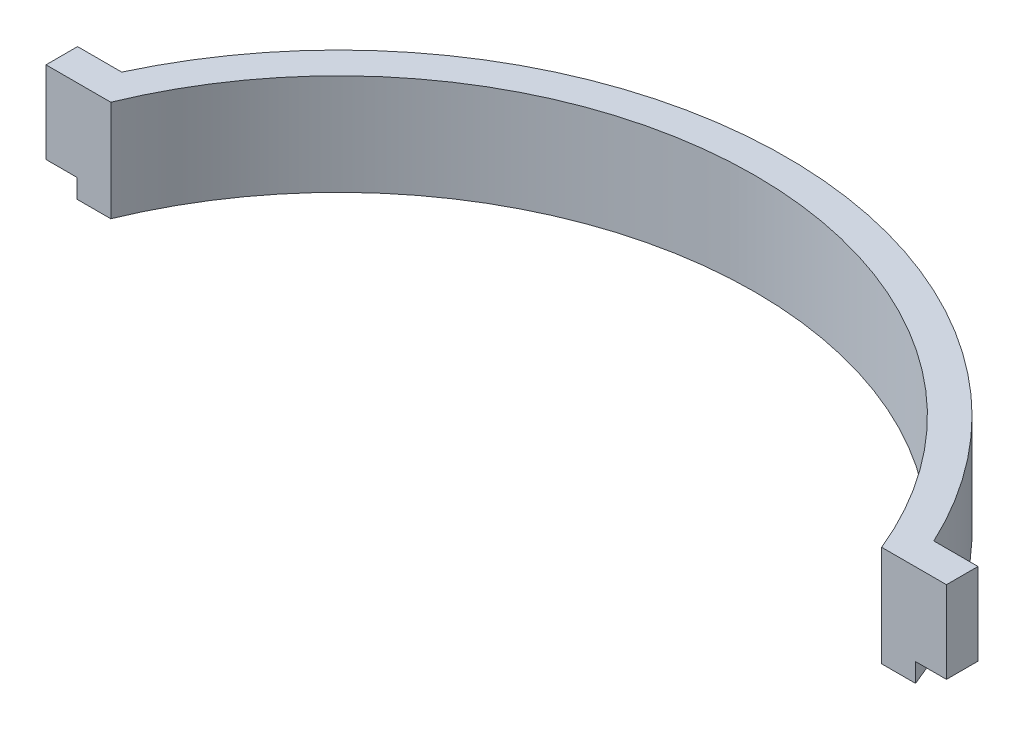
SolidWorks part; units mm, degrees
ref_plane "Front Plane" through (0, 0, 0) normal (0, 0, 1) x (1, 0, 0)
ref_plane "Top Plane" through (0, 0, 0) normal (0, 1, 0) x (1, 0, 0)
ref_plane "Right Plane" through (0, 0, 0) normal (1, 0, 0) x (0, 0, -1)
sketch "Sketch2" plane through (0, 0, 0) normal (0, 1, 0) x (1, 0, 0)
  line L0 (-71.3506, 25) -> (-61.0819, 25)
  line L1 (61.0819, 25) -> (71.3506, 25)
  line L2 (-71.3506, 25) -> (-71.3506, 30)
  line L3 (-71.3506, 30) -> (-64.3506, 30)
  line L4 (64.3506, 30) -> (71.3506, 30)
  line L5 (71.3506, 30) -> (71.3506, 25)
  line L6 (0, 66) -> (0, 71) construction
  arc A0 (-61.0819, 25) -> (61.0819, 25) centre (0, 0) cw
  arc A1 (-64.3506, 30) -> (64.3506, 30) centre (0, 0) cw
  dimension "D1" = 66
  dimension "D2" = 5
  dimension "D3" = 7
  dimension "D4" = 25
extrude "Boss-Extrude1" add sketch "Sketch2" along normal blind 13
sketch "Sketch3" plane through (0, 0, 0) normal (0, -1, 0) x (1, 0, 0)
  line L0 (-71.3506, -25) -> (-61.0819, -25) construction
  line L1 (61.0819, -25) -> (71.3506, -25) construction
  line L2 (66.453, -25) -> (61.0819, -25)
  line L3 (-66.453, -25) -> (-61.0819, -25)
  arc A0 (-61.0819, -25) -> (61.0819, -25) centre (0, 0) ccw construction
  arc A1 (-61.0819, -25) -> (61.0819, -25) centre (0, 0) ccw
  arc A2 (-66.453, -25) -> (66.453, -25) centre (0, 0) ccw
  arc A3 (-64.3506, -30) -> (64.3506, -30) centre (0, 0) ccw construction
extrude "Boss-Extrude2" add sketch "Sketch3" along normal blind 3
